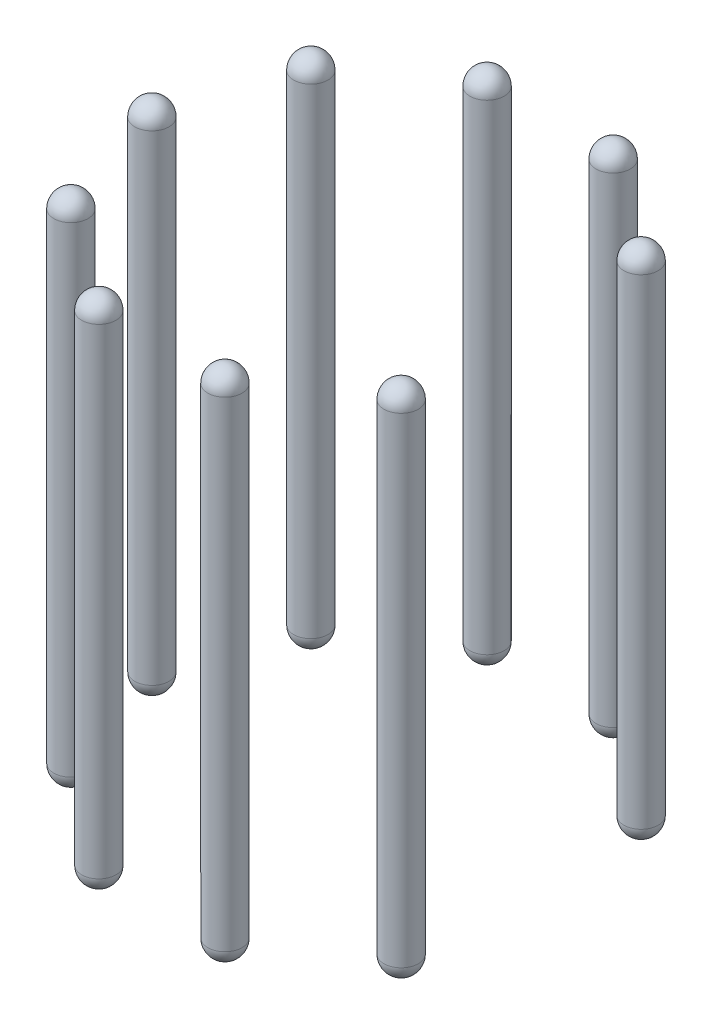
SolidWorks part; units mm, degrees
material "Pure Gold"
ref_plane "Front Plane" through (0, 0, 0) normal (0, 0, 1) x (1, 0, 0)
ref_plane "Top Plane" through (0, 0, 0) normal (0, 1, 0) x (1, 0, 0)
ref_plane "Right Plane" through (0, 0, 0) normal (1, 0, 0) x (0, 0, -1)
ref_plane "Plane1" through (0, 0, 0) normal (0.5878, 0, 0.809) x (0.809, 0, -0.5878)
sketch "Sketch1" plane through (0, 0, 0) normal (0.5878, 0, 0.809) x (0.809, 0, -0.5878)
  line L0 (6.45, 8) -> (6.45, -6)
  line L1 (5.95, -6.5) -> (5.95, 8.5)
  line L2 (5.95, -7.25) -> (5.95, 9.25) construction
  arc A0 (6.45, 8) -> (5.95, 8.5) centre (5.95, 8) ccw
  arc A1 (5.95, -6.5) -> (6.45, -6) centre (5.95, -6) ccw
revolve "Revolve1" add sketch "Sketch1" angle 360 about L2
ref_plane "Plane2" through (0, 0, 0) normal (0.9511, 0, 0.309) x (0.309, 0, -0.9511)
sketch "Sketch2" plane through (0, 0, 0) normal (0.9511, 0, 0.309) x (0.309, 0, -0.9511)
  line L0 (6.45, 8) -> (6.45, -6)
  line L1 (5.95, -6.5) -> (5.95, 8.5)
  line L2 (5.95, -7.25) -> (5.95, 9.25) construction
  arc A0 (6.45, 8) -> (5.95, 8.5) centre (5.95, 8) ccw
  arc A1 (5.95, -6.5) -> (6.45, -6) centre (5.95, -6) ccw
revolve "Revolve2" add sketch "Sketch2" angle 360 about L2
ref_plane "Plane3" through (0, 0, 0) normal (0.9511, 0, -0.309) x (-0.309, 0, -0.9511)
sketch "Sketch3" plane through (0, 0, 0) normal (0.9511, 0, -0.309) x (-0.309, 0, -0.9511)
  line L0 (6.45, 8) -> (6.45, -6)
  line L1 (5.95, -6.5) -> (5.95, 8.5)
  line L2 (5.95, -7.25) -> (5.95, 9.25) construction
  arc A0 (6.45, 8) -> (5.95, 8.5) centre (5.95, 8) ccw
  arc A1 (5.95, -6.5) -> (6.45, -6) centre (5.95, -6) ccw
revolve "Revolve3" add sketch "Sketch3" angle 360 about L2
ref_plane "Plane4" through (0, 0, 0) normal (0.5878, 0, -0.809) x (-0.809, 0, -0.5878)
sketch "Sketch4" plane through (0, 0, 0) normal (0.5878, 0, -0.809) x (-0.809, 0, -0.5878)
  line L0 (6.45, 8) -> (6.45, -6)
  line L1 (5.95, -6.5) -> (5.95, 8.5)
  line L2 (5.95, -7.25) -> (5.95, 9.25) construction
  arc A0 (6.45, 8) -> (5.95, 8.5) centre (5.95, 8) ccw
  arc A1 (5.95, -6.5) -> (6.45, -6) centre (5.95, -6) ccw
revolve "Revolve4" add sketch "Sketch4" angle 360 about L2
ref_plane "Plane5" through (0, 0, 0) normal (0, 0, -1) x (-1, 0, 0)
sketch "Sketch5" plane through (0, 0, 0) normal (0, 0, -1) x (-1, 0, 0)
  line L0 (6.45, 8) -> (6.45, -6)
  line L1 (5.95, -6.5) -> (5.95, 8.5)
  line L2 (5.95, -7.25) -> (5.95, 9.25) construction
  arc A0 (6.45, 8) -> (5.95, 8.5) centre (5.95, 8) ccw
  arc A1 (5.95, -6.5) -> (6.45, -6) centre (5.95, -6) ccw
revolve "Revolve5" add sketch "Sketch5" angle 360 about L2
ref_plane "Plane6" through (0, 0, 0) normal (-0.5878, 0, -0.809) x (-0.809, 0, 0.5878)
sketch "Sketch6" plane through (0, 0, 0) normal (-0.5878, 0, -0.809) x (-0.809, 0, 0.5878)
  line L0 (6.45, 8) -> (6.45, -6)
  line L1 (5.95, -6.5) -> (5.95, 8.5)
  line L2 (5.95, -7.25) -> (5.95, 9.25) construction
  arc A0 (6.45, 8) -> (5.95, 8.5) centre (5.95, 8) ccw
  arc A1 (5.95, -6.5) -> (6.45, -6) centre (5.95, -6) ccw
revolve "Revolve6" add sketch "Sketch6" angle 360 about L2
ref_plane "Plane7" through (0, 0, 0) normal (-0.9511, 0, -0.309) x (-0.309, 0, 0.9511)
sketch "Sketch7" plane through (0, 0, 0) normal (-0.9511, 0, -0.309) x (-0.309, 0, 0.9511)
  line L0 (6.45, 8) -> (6.45, -6)
  line L1 (5.95, -6.5) -> (5.95, 8.5)
  line L2 (5.95, -7.25) -> (5.95, 9.25) construction
  arc A0 (6.45, 8) -> (5.95, 8.5) centre (5.95, 8) ccw
  arc A1 (5.95, -6.5) -> (6.45, -6) centre (5.95, -6) ccw
revolve "Revolve7" add sketch "Sketch7" angle 360 about L2
ref_plane "Plane8" through (0, 0, 0) normal (-0.9511, 0, 0.309) x (0.309, 0, 0.9511)
sketch "Sketch8" plane through (0, 0, 0) normal (-0.9511, 0, 0.309) x (0.309, 0, 0.9511)
  line L0 (6.45, 8) -> (6.45, -6)
  line L1 (5.95, -6.5) -> (5.95, 8.5)
  line L2 (5.95, -7.25) -> (5.95, 9.25) construction
  arc A0 (6.45, 8) -> (5.95, 8.5) centre (5.95, 8) ccw
  arc A1 (5.95, -6.5) -> (6.45, -6) centre (5.95, -6) ccw
revolve "Revolve8" add sketch "Sketch8" angle 360 about L2
ref_plane "Plane9" through (0, 0, 0) normal (-0.5878, 0, 0.809) x (0.809, 0, 0.5878)
sketch "Sketch9" plane through (0, 0, 0) normal (-0.5878, 0, 0.809) x (0.809, 0, 0.5878)
  line L0 (6.45, 8) -> (6.45, -6)
  line L1 (5.95, -6.5) -> (5.95, 8.5)
  line L2 (5.95, -7.25) -> (5.95, 9.25) construction
  arc A0 (6.45, 8) -> (5.95, 8.5) centre (5.95, 8) ccw
  arc A1 (5.95, -6.5) -> (6.45, -6) centre (5.95, -6) ccw
revolve "Revolve9" add sketch "Sketch9" angle 360 about L2
